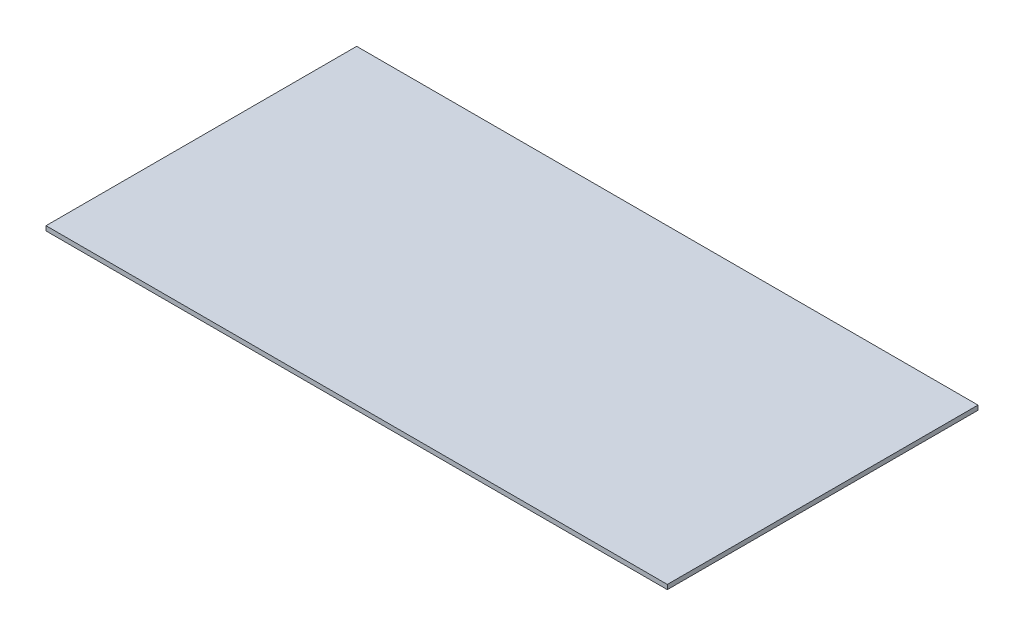
SolidWorks part; units mm, degrees
ref_plane "Front Plane" through (0, 0, 0) normal (0, 0, 1) x (1, 0, 0)
ref_plane "Top Plane" through (0, 0, 0) normal (0, 1, 0) x (1, 0, 0)
ref_plane "Right Plane" through (0, 0, 0) normal (1, 0, 0) x (0, 0, -1)
sketch "Sketch2" plane through (0, 0, 0) normal (0, 1, 0) x (1, 0, 0)
  line L1 (-1219.2, 609.6) -> (1219.2, 609.6)
  line L2 (-1219.2, 609.6) -> (-1219.2, -609.6)
  line L3 (-1219.2, -609.6) -> (1219.2, -609.6)
  line L4 (1219.2, 609.6) -> (1219.2, -609.6)
  line L5 (-1219.2, 609.6) -> (1219.2, -609.6) construction
  line L6 (-1219.2, -609.6) -> (1219.2, 609.6) construction
  point P0 (0, 0)
  dimension "D1" = 2438.4
  dimension "D2" = 1219.2
extrude "Boss-Extrude1" add sketch "Sketch2" along normal blind 8.9281 and the other way blind 8.9281
